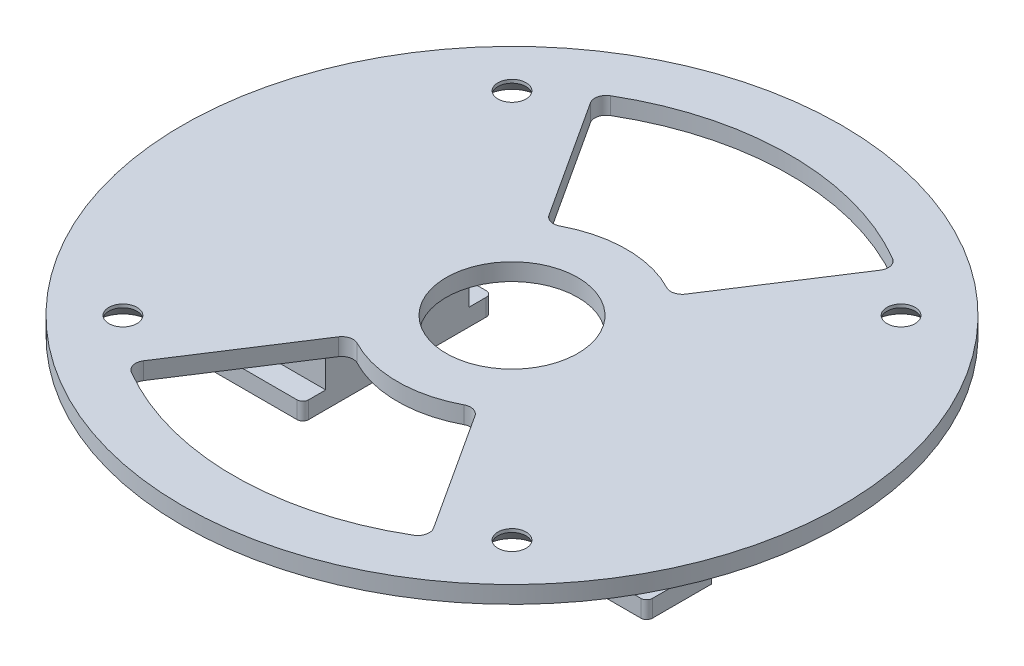
SolidWorks part; units mm, degrees
material "ABS"
ref_plane "Front Plane" through (0, 0, 0) normal (0, 0, 1) x (1, 0, 0)
ref_plane "Top Plane" through (0, 0, 0) normal (0, 1, 0) x (1, 0, 0)
ref_plane "Right Plane" through (0, 0, 0) normal (1, 0, 0) x (0, 0, -1)
sketch "Sketch1" plane through (0, 0, 0) normal (0, 1, 0) x (1, 0, 0)
  line L0 (0, 57.5) -> (0, 0) construction
  line L1 (0, 0) -> (-57.5, 0) construction
  line L2 (-57.5, 0) -> (-40.6586, 40.6586) construction
  line L3 (-40.6586, 40.6586) -> (0, 57.5) construction
  line L4 (-40.6586, 40.6586) -> (0, 0) construction
  line L5 (-3, 4.9375) -> (6.3, 4.9375)
  line L7 (-3, 4.9375) -> (-3, -4.9375)
  line L8 (-3, -4.9375) -> (6.3, -4.9375)
  line L9 (6.3, 4.9375) -> (6.3, -4.9375)
  line L14 (-3, -4.9375) -> (6.3, -4.9375) construction
  circle A0 centre (0, 0) radius 57.5
  circle A1 centre (-33.9411, 33.9411) radius 0.5
  circle A2 centre (33.9411, 33.9411) radius 0.5
  circle A3 centre (33.9411, -33.9411) radius 0.5
  circle A4 centre (-33.9411, -33.9411) radius 0.5
  point P17 (0, 0)
  dimension "D2" = 115
  dimension "D3" = 1
  dimension "D1" = 48
  dimension "D5" = 9.875
  dimension "D7" = 9.3
  dimension "D6" = 3
  dimension "D4" = 4
extrude "Boss-Extrude1" add sketch "Sketch1" along normal blind 3
hole_wizard "CSK for #8 Flat Head Socket Cap Screw1" positions "Sketch3" profile "Sketch2" countersink size "#8" standard "ANSI Inch" end condition through all
sketch "Sketch3" plane through (0, 0, 0) normal (0, -1, 0) x (-1, 0, 0)
  point P0 (33.9411, -33.9411)
  point P3 (-33.9411, -33.9411)
  point P6 (-33.9411, 33.9411)
  point P9 (33.9411, 33.9411)
sketch "Sketch2" plane through (-33.9411, 0, 33.9411) normal (1, 0, 0) x (0, 0, -1)
  line L0 (0, 0) -> (0, 3)
  line L1 (0, 3) -> (2.4574, 3)
  line L2 (2.4574, 3) -> (2.4574, 2.4179)
  line L3 (2.4574, 2.4179) -> (4.5593, 0)
  line L5 (4.5593, 0) -> (0, 0)
  line L6 (-2.4575, 2.4179) -> (-4.5593, 0) construction
  line L11 (0, -6.35) -> (0, 107.95) construction
  dimension "Thru Hole Dia." = 4.9149
  dimension "Thru Hole Depth" = 3
  dimension "Near C'Sink Dia." = 9.1186
  dimension "Near C'Sink Angle" = 82
sketch "Sketch5" plane through (0, 0, 0) normal (0, -1, 0) x (1, 0, 0)
  line L0 (1.65, -4.9375) -> (1.65, 4.9375) construction
  line L1 (6.3, -4.9375) -> (10.3625, -4.9375)
  line L2 (6.3, -4.9375) -> (6.3, 4.9375)
  line L3 (6.3, 4.9375) -> (10.3625, 4.9375)
  line L4 (10.3625, -4.9375) -> (10.3625, 4.9375)
  line L5 (6.3, -4.9375) -> (-3, -4.9375) construction
  line L6 (-3, 4.9375) -> (6.3, 4.9375) construction
  line L7 (-7.0625, -4.9375) -> (-7.0625, 4.9375)
  line L8 (-3, 4.9375) -> (-7.0625, 4.9375)
  line L9 (-3, -4.9375) -> (-3, 4.9375)
  line L10 (-3, -4.9375) -> (-7.0625, -4.9375)
  dimension "D1" = 4.0625
extrude "Cut-Extrude2" cut sketch "Sketch5" against normal through all
sketch "Sketch6" plane through (0, 0, 0) normal (0, -1, 0) x (1, 0, 0)
  line L0 (-57.5, 0) -> (57.5, 0) construction
  line L1 (0, -57.5) -> (0, 57.5) construction
  line L2 (-20, -12.5) -> (-20, 12.5)
  line L3 (-40, -12.5) -> (-20, -12.5)
  line L4 (-40, -12.5) -> (-40, 12.5)
  line L5 (-40, 12.5) -> (-20, 12.5)
  line L6 (40, -12.5) -> (40, 12.5)
  line L7 (20, -12.5) -> (20, 12.5)
  line L8 (20, -12.5) -> (40, -12.5)
  line L9 (20, 12.5) -> (40, 12.5)
  circle A0 centre (0, 0) radius 57.5 construction
  dimension "D1" = 25
  dimension "D2" = 80
  dimension "D3" = 20
extrude "Boss-Extrude2" add sketch "Sketch6" along normal blind 15
sketch "Sketch7" plane through (0, 0, 12.5) normal (0, 0, 1) x (1, 0, 0)
  line L0 (-40, -7.5) -> (40, -7.5) construction
  line L1 (-40, -15) -> (-40, 0) construction
  line L2 (40, -15) -> (40, 0) construction
  line L3 (0, 0) -> (0, -28.8588) construction
  line L4 (-20, 0) -> (-40, 0) construction
  circle A0 centre (-32.25, -6.75) radius 4.75 construction
  circle A1 centre (-32.25, -6.75) radius 4.425
  circle A2 centre (32.25, -6.75) radius 4.425
  dimension "D1" = 9.5
  dimension "D3" = 8.85
  dimension "D2" = 7.75
  dimension "D4" = 6.75
extrude "Cut-Extrude3" cut sketch "Sketch7" against normal through all
sketch "Sketch8" plane through (-40, 0, 0) normal (-1, 0, 0) x (0, 0, 1)
  line L0 (0, 0) -> (0, -15) construction
  line L1 (12.5, 0) -> (-12.5, 0) construction
  line L2 (12.5, -15) -> (-12.5, -15) construction
  line L3 (-12.5, -15) -> (-12.5, 0) construction
  line L4 (-16.5, -12) -> (16.5, -12)
  line L5 (-16.5, -12) -> (-16.5, -15)
  line L6 (-16.5, -15) -> (16.5, -15)
  line L7 (16.5, -12) -> (16.5, -15)
  dimension "D1" = 3
  dimension "D2" = 4
extrude "Boss-Extrude3" add sketch "Sketch8" against normal up to surface (20 mm away) up to face at (-20, -7.5, 0)
sketch "Sketch9" plane through (40, 0, 0) normal (1, 0, 0) x (0, 0, -1)
  line L0 (16.5, -15) -> (-16.5, -15) construction
  line L1 (16.5, -15) -> (-16.5, -15)
  line L2 (16.5, -15) -> (16.5, -12) construction
  line L5 (-16.5, -12) -> (-16.5, -15) construction
  line L6 (16.5, -15) -> (16.5, -12)
  line L7 (16.5, -12) -> (-16.5, -12)
  line L9 (-16.5, -12) -> (-16.5, -15)
extrude "Boss-Extrude4" add sketch "Sketch9" against normal up to surface (20 mm away) up to face at (20, -7.5, 0)
fillet "Fillet1" radius 1 8 edges at (-20, -13.5, 16.5) (-40, -13.5, 16.5) (-20, -13.5, -16.5) (-40, -13.5, -16.5) (20, -13.5, 16.5) (20, -13.5, -16.5) (40, -13.5, 16.5) (40, -13.5, -16.5)
fillet "Fillet2" radius 5 4 edges at (-40, 0, 0) (40, 0, 0) (-20, 0, 0) (20, 0, 0)
sketch "Sketch10" plane through (0, 0, 0) normal (0, -1, 0) x (1, 0, 0)
  line L0 (0, 57.5) -> (0, 0) construction
  line L1 (0, 0) -> (57.5, 0) construction
  line L2 (26.3975, 40.6869) -> (10.8855, 16.7781)
  line L3 (-26.3975, 40.6869) -> (-10.8855, 16.7781)
  line L4 (0, 0) -> (10.8855, 16.7781) construction
  line L5 (0, 0) -> (-10.8855, 16.7781) construction
  line L6 (-26.3975, -40.6869) -> (-10.8855, -16.7781)
  line L7 (26.3975, -40.6869) -> (10.8855, -16.7781)
  circle A0 centre (0, 0) radius 57.5 construction
  arc A1 (26.3975, 40.6869) -> (-26.3975, 40.6869) centre (0, 0) ccw
  arc A2 (33.9411, 33.9411) -> (-34.0273, 33.8547) centre (0, 0) ccw construction
  arc A3 (10.8855, 16.7781) -> (-10.8855, 16.7781) centre (0, 0) ccw
  arc A4 (10.8855, -16.7781) -> (-10.8855, -16.7781) centre (0, 0) cw
  arc A5 (26.3975, -40.6869) -> (-26.3975, -40.6869) centre (0, 0) cw
  dimension "D1" = 9
  dimension "D2" = 20
  dimension "D3" = 10
extrude "Cut-Extrude4" cut sketch "Sketch10" against normal through all
fillet "Fillet3" radius 2 8 edges at (26.3975, 1.5, -40.6869) (-26.3975, 1.5, -40.6869) (10.8855, 1.5, -16.7781) (-10.8855, 1.5, -16.7781) (-26.3975, 1.5, 40.6869) (-10.8855, 1.5, 16.7781) (10.8855, 1.5, 16.7781) (26.3975, 1.5, 40.6869)
sketch "Sketch11" plane through (0, -15, 0) normal (0, -1, 0) x (1, 0, 0)
  line L0 (-40, 0) -> (40, 0) construction
  line L1 (-40, 15.5) -> (-40, -15.5) construction
  line L2 (40, -15.5) -> (40, 15.5) construction
  line L3 (0, 0) -> (0, 69.3624) construction
  line L4 (-40, -5.15) -> (-36.7, -5.15)
  line L5 (-40, -5.15) -> (-40, 5.15)
  line L6 (-40, 5.15) -> (-36.7, 5.15)
  line L7 (-36.7, -5.15) -> (-36.7, 5.15)
  line L8 (36.7, -5.15) -> (36.7, 5.15)
  line L9 (40, 5.15) -> (36.7, 5.15)
  line L10 (40, -5.15) -> (40, 5.15)
  line L11 (40, -5.15) -> (36.7, -5.15)
  dimension "D1" = 10.3
  dimension "D2" = 3.3
extrude "Cut-Extrude5" cut sketch "Sketch11" against normal blind 3.3
sketch "Sketch12" plane through (0, 0, 0) normal (0, -1, 0) x (1, 0, 0)
  circle A0 centre (0, 0) radius 11.4787
extrude "Cut-Extrude6" cut sketch "Sketch12" against normal through all
equation "\"D6@Sketch1\"=\"width keep@values@params_print.sldprt\""
equation "\"D7@Sketch1\"=\"pin diameter@values@params_print.sldprt\"+2*\"width keep@values@params_print.sldprt\"+\"print fit@values@params_print.sldprt\""
equation "\"D5@Sketch1\"=9.75 +\"print fit@values@params_print.sldprt\""
equation "\"D1@Boss-Extrude1\"=\"width keep@values@params_print.sldprt\""
equation "\"D1@Sketch5\" = \"width tab@values@params_print.sldprt\" + \"print fit@values@params_print.sldprt\" / 2"
equation "\"D2@Sketch8\"=\"width tab@values@params_print.sldprt\""
equation "\"D4@Sketch7\"=9.5/2+2"
equation "\"D1@Sketch11\"=10+\"print free@values@params_print.sldprt\""
equation "\"D2@Sketch11\"=3+\"print free@values@params_print.sldprt\""
